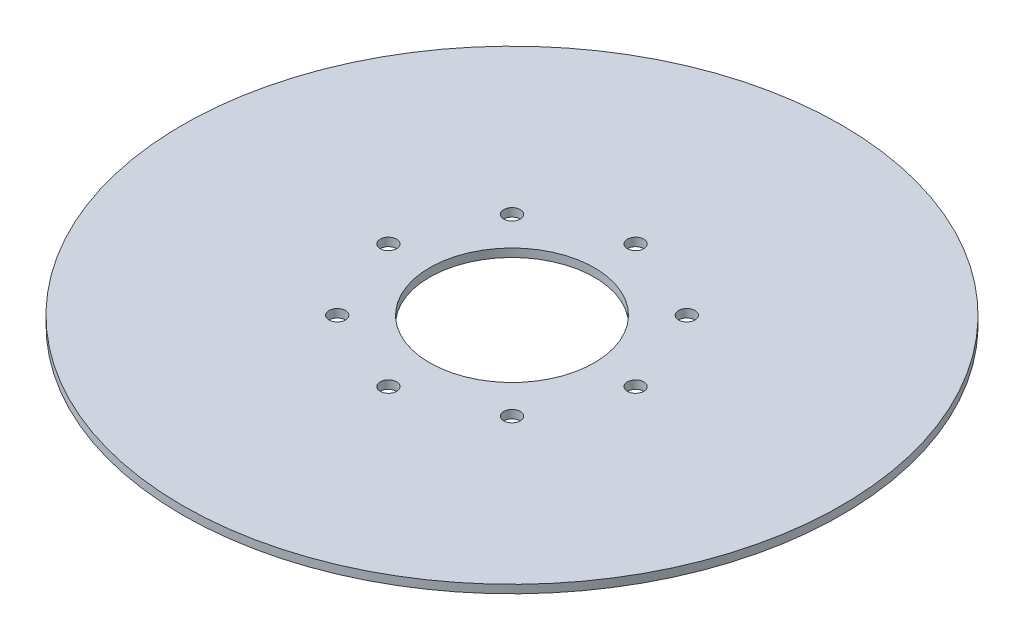
SolidWorks part; units mm, degrees
ref_plane "Front Plane" through (0, 0, 0) normal (0, 0, 1) x (1, 0, 0)
ref_plane "Top Plane" through (0, 0, 0) normal (0, 1, 0) x (1, 0, 0)
ref_plane "Right Plane" through (0, 0, 0) normal (1, 0, 0) x (0, 0, -1)
sketch "Sketch2" plane through (0, 0, 0) normal (0, 1, 0) x (1, 0, 0)
  circle A0 centre (0, 0) radius 40
extrude "Boss-Extrude1" add sketch "Sketch2" along normal blind 1
sketch "Sketch3" plane through (0, 1, 0) normal (0, 1, 0) x (1, 0, 0)
  circle A0 centre (0, 0) radius 10
extrude "Cut-Extrude1" cut sketch "Sketch3" against normal through all
sketch "Sketch4" plane through (0, 1, 0) normal (0, 1, 0) x (1, 0, 0)
  circle A0 centre (0, 15) radius 1
  circle A1 centre (10.6066, 10.6066) radius 1
  circle A2 centre (15, 0) radius 1
  circle A3 centre (10.6066, -10.6066) radius 1
  circle A4 centre (0, -15) radius 1
  circle A5 centre (-10.6066, -10.6066) radius 1
  circle A6 centre (-15, 0) radius 1
  circle A7 centre (-10.6066, 10.6066) radius 1
  point P18 (0, 0)
  dimension "D1" = 8
  dimension "D2" = 15
extrude "Cut-Extrude2" cut sketch "Sketch4" against normal through all
